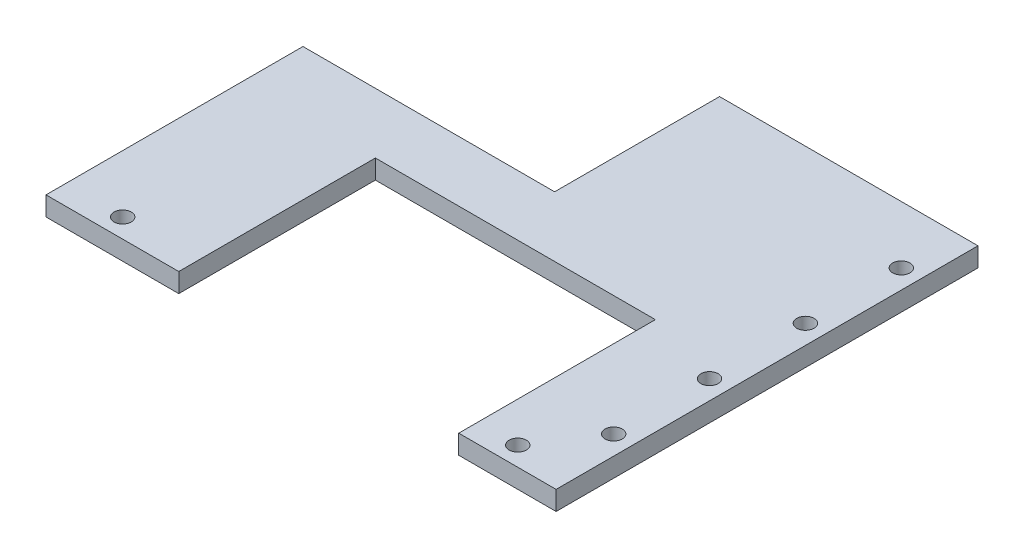
SolidWorks part; units mm, degrees
ref_plane "Front Plane" through (0, 0, 0) normal (0, 0, 1) x (1, 0, 0)
ref_plane "Top Plane" through (0, 0, 0) normal (0, 1, 0) x (1, 0, 0)
ref_plane "Right Plane" through (0, 0, 0) normal (1, 0, 0) x (0, 0, -1)
sketch "Sketch1" plane through (0, 0, 0) normal (0, 1, 0) x (1, 0, 0)
  line L0 (0, 55.7333) -> (0, 12.7333)
  line L1 (0, 55.7333) -> (67.3866, 55.7333)
  line L2 (-65.6134, 12.7333) -> (-65.6134, -54.2667)
  line L3 (-65.6134, -54.2667) -> (67.3866, -54.2667)
  line L4 (67.3866, 55.7333) -> (67.3866, -54.2667)
  line L5 (-15.8117, 12.7333) -> (67.3866, -54.2667) construction
  line L6 (-65.6134, -54.2667) -> (67.3866, 55.7333) construction
  line L7 (0, 12.7333) -> (-65.6134, 12.7333)
  line L8 (57.3866, 55.7333) -> (57.3866, -54.2667) construction
  line L9 (62.3866, 55.7333) -> (62.3866, -54.2667) construction
  line L10 (57.3866, 0.7333) -> (67.3866, 0.7333) construction
  line L11 (-65.6134, -44.2667) -> (67.3866, -44.2667) construction
  line L12 (-65.6134, -49.2667) -> (67.3866, -49.2667) construction
  line L13 (0.8866, -54.2667) -> (0.8866, -44.2667) construction
  circle A0 centre (62.3866, 40.7333) radius 2.25
  circle A1 centre (62.3866, 15.7333) radius 2.25
  circle A2 centre (62.3866, -9.2667) radius 2.25
  circle A3 centre (62.3866, -34.2667) radius 2.25
  circle A4 centre (0.8866, -49.2667) radius 2.25
  circle A5 centre (-50.6134, -49.2667) radius 2.25
  circle A6 centre (52.3866, -49.2667) radius 2.25
  point P0 (0, 0)
  point P6 (-65.6134, 12.7333)
  point P7 (0, 55)
  point P14 (57.3866, 55.7333)
  point P18 (62.3866, 40.7333)
  dimension "D7" = 4
  dimension "D10" = 4.5
  dimension "D11" = 15
  dimension "D1" = 67
  dimension "D2" = 110
  dimension "D3" = 133
  dimension "D4" = 10
  dimension "D5" = 5
  dimension "D6" = 15
  dimension "D8" = 10
  dimension "D9" = 5
extrude "Boss-Extrude1" add sketch "Sketch1" along normal blind 5
sketch "Sketch2" plane through (0, 5, 0) normal (0, 1, 0) x (1, 0, 0)
  line L0 (23.1465, -3) -> (23.1465, -55) construction
  line L2 (67.3866, -54.2667) -> (67.3866, 55.7333) construction
  line L3 (-65.6134, -54.2667) -> (67.3866, -54.2667) construction
  line L4 (-8, -3) -> (42, -3)
  line L6 (-8, -54.2667) -> (42, -54.2667)
  line L7 (42, -3) -> (42, -54.2667)
  line L8 (-31, -3) -> (-8, -3)
  line L9 (-31, -3) -> (-31, -54.2667)
  line L10 (-31, -54.2667) -> (-8, -54.2667)
  point P0 (23.1465, -3)
  point P3 (-8, -3)
  point P6 (44.3866, -3)
  point P13 (-31, -3)
  dimension "D1" = 52
  dimension "D2" = 73
  dimension "D3" = 23
extrude "Cut-Extrude1" cut sketch "Sketch2" against normal blind 5
